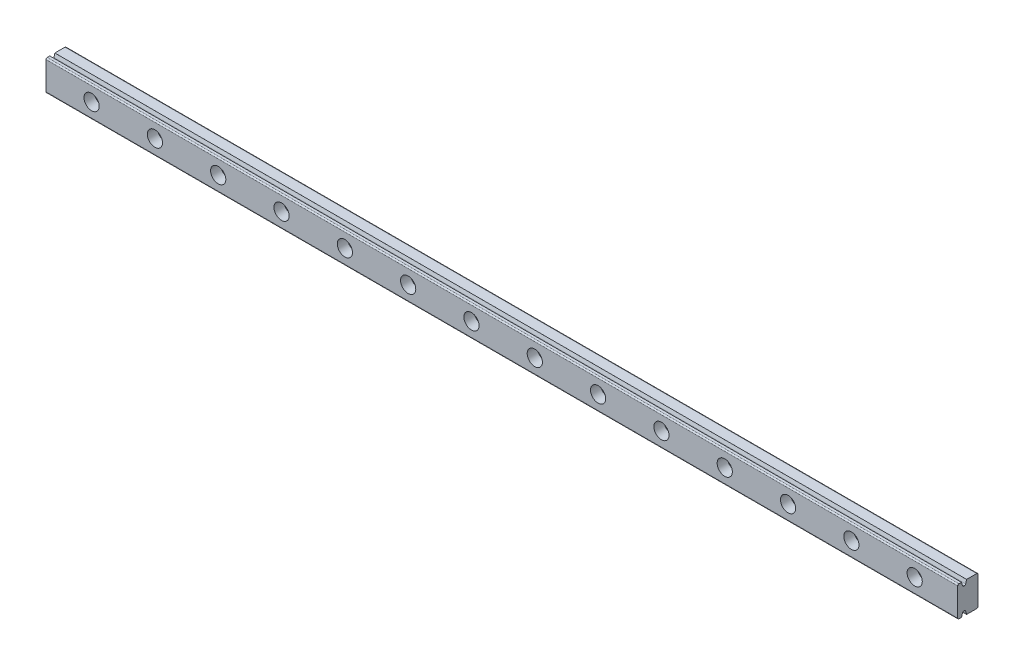
SolidWorks part; units mm, degrees
ref_plane "Front Plane" through (0, 0, 0) normal (0, 0, 1) x (1, 0, 0)
ref_plane "Top Plane" through (0, 0, 0) normal (0, 1, 0) x (1, 0, 0)
ref_plane "Right Plane" through (0, 0, 0) normal (1, 0, 0) x (0, 0, -1)
sketch "Sketch1" plane through (0, 0, 0) normal (1, 0, 0) x (0, 0, -1)
  line L0 (-0.5, 6) -> (4, 6)
  line L1 (-4, 6) -> (-2.5, 6)
  line L2 (-4, 6) -> (-4, -6)
  line L3 (-4, -6) -> (-2.5, -6)
  line L4 (4, 6) -> (4, -6)
  line L5 (-4, 6) -> (4, -6) construction
  line L6 (-4, -6) -> (4, 6) construction
  line L8 (-2.5, 6) -> (-2.5, 4.25)
  line L9 (-2.5, 4.25) -> (-0.5, 4.25)
  line L10 (-0.5, 6) -> (-0.5, 4.25)
  line L12 (-2.5, -6) -> (-2.5, -4.25)
  line L13 (-2.5, -4.25) -> (-0.5, -4.25)
  line L14 (-0.5, -6) -> (-0.5, -4.25)
  line L15 (-0.5, -6) -> (4, -6)
  point P0 (0, 0)
  dimension "D1" = 12
  dimension "D2" = 8
  dimension "D3" = 2
  dimension "D4" = 2
  dimension "D5" = 1.5
  dimension "D6" = 1.5
  dimension "D7" = 8.5
  dimension "D8" = 4.25
extrude "Boss-Extrude1" add sketch "Sketch1" along normal blind 450
sketch "Sketch2" plane through (0, 0, 4) normal (0, 0, 1) x (1, 0, 0)
  line L0 (0, 6) -> (0, -6) construction
  circle A0 centre (13, 0) radius 1.75
  circle A1 centre (38, 0) radius 1.75
  circle A2 centre (63, 0) radius 1.75
  circle A3 centre (88, 0) radius 1.75
  circle A4 centre (113, 0) radius 1.75
  circle A5 centre (138, 0) radius 1.75
  circle A6 centre (163, 0) radius 1.75
  circle A7 centre (188, 0) radius 1.75
  circle A8 centre (213, 0) radius 1.75
  circle A9 centre (238, 0) radius 1.75
  circle A10 centre (263, 0) radius 1.75
  circle A11 centre (288, 0) radius 1.75
  circle A12 centre (313, 0) radius 1.75
  circle A13 centre (338, 0) radius 1.75
  circle A14 centre (363, 0) radius 1.75
  circle A15 centre (388, 0) radius 1.75
  circle A16 centre (413, 0) radius 1.75
  circle A17 centre (438, 0) radius 1.75
  dimension "D1" = 3.5
  dimension "D2" = 13
  dimension "D3" = 18
extrude "Cut-Extrude1" cut sketch "Sketch2" against normal blind 10
sketch "Sketch3" plane through (0, 0, 4) normal (0, 0, 1) x (1, 0, 0)
  circle A0 centre (13, 0) radius 3
  circle A1 centre (38, 0) radius 3
  circle A2 centre (63, 0) radius 3
  circle A3 centre (88, 0) radius 3
  circle A4 centre (113, 0) radius 3
  circle A5 centre (138, 0) radius 3
  circle A6 centre (163, 0) radius 3
  circle A7 centre (188, 0) radius 3
  circle A8 centre (213, 0) radius 3
  circle A9 centre (238, 0) radius 3
  circle A10 centre (263, 0) radius 3
  circle A11 centre (288, 0) radius 3
  circle A12 centre (313, 0) radius 3
  circle A13 centre (338, 0) radius 3
  circle A14 centre (363, 0) radius 3
  circle A15 centre (388, 0) radius 3
  circle A16 centre (413, 0) radius 3
  circle A17 centre (438, 0) radius 3
  dimension "D1" = 6
  dimension "D2" = 18
extrude "Cut-Extrude2" cut sketch "Sketch3" against normal blind 4
chamfer "Chamfer1" distance 0.5 angle 74 4 edges at (225, -4.25, 2.5) (225, -4.25, 0.5) (225, 4.25, 2.5) (225, 4.25, 0.5)
fillet "Fillet1" radius 0.5 20 edges at (450, -6, -1.75) (450, 0, -4) (450, 6, -1.75) (450, 6, 3.25) (450, 0, 4) (450, -6, 3.25) (0, -6, 3.25) (0, -6, -1.75) (0, 0, -4) (0, 6, -1.75) (0, 6, 3.25) (0, 0, 4) (225, -4.25, 1) (225, -4.25, 2) (225, 4.25, 2) (225, 4.25, 1) (225, -6, 4) (225, 6, 4) (225, -6, -4) (225, 6, -4)
sketch "Sketch4" plane through (0, 0, 4) normal (0, 0, 1) x (1, 0, 0)
  line L0 (0, -5.5) -> (0, 5.5) construction
  line L1 (0, 68.4613) -> (45, 68.4613)
  line L2 (0, 68.4613) -> (0, -111.7992)
  line L3 (0, -111.7992) -> (45, -111.7992)
  line L4 (45, 68.4613) -> (45, -111.7992)
  line L5 (450, -121.2204) -> (405, -121.2204)
  line L6 (450, -121.2204) -> (450, 167.0707)
  line L7 (450, 167.0707) -> (405, 167.0707)
  line L8 (405, -121.2204) -> (405, 167.0707)
  line L9 (450, 5.5) -> (450, -5.5) construction
  point P13 (450, 0)
  dimension "D1" = 0
  dimension "D2" = 45
  dimension "D3" = 0
  dimension "D4" = 45
extrude "Cut-Extrude3" cut sketch "Sketch4" against normal through all both and the other way through all
